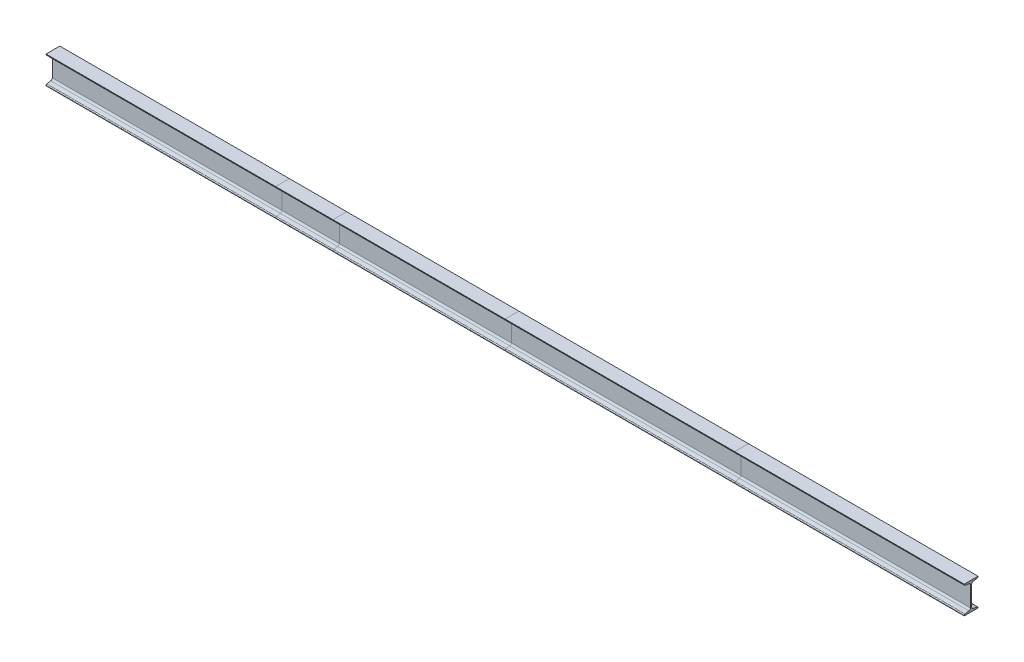
SolidWorks part; units mm, degrees
ref_plane "Front Plane" through (0, 0, 0) normal (0, 0, 1) x (1, 0, 0)
ref_plane "Top Plane" through (0, 0, 0) normal (0, 1, 0) x (1, 0, 0)
ref_plane "Right Plane" through (0, 0, 0) normal (1, 0, 0) x (0, 0, -1)
sketch "Sketch1" plane through (0, 0, 0) normal (0, 0, 1) x (1, 0, 0)
  line L0 (0, 0) -> (1000, 0)
  line L1 (1000, 0) -> (1250, 0)
  line L2 (1250, 0) -> (2000, 0)
  line L3 (2000, 0) -> (3000, 0)
  line L4 (3000, 0) -> (4000, 0)
  dimension "D1" = 1000
  dimension "D2" = 250
  dimension "D3" = 750
  dimension "D4" = 1000
  dimension "D5" = 1000
other "Sb beam 120 X 12(1)"
ref_plane "Plane1" through (0, 0, 0) normal (1, 0, 0) x (0, 0, 1)
sketch "Sketch11" plane through (0, 0, 0) normal (1, 0, 0) x (0, 0, 1)
  line L0 (-30, -60) -> (-30, -58.0801)
  line L1 (-26.6576, -54.1345) -> (-9.1847, -51.2221)
  line L2 (-2.5, -43.331) -> (-2.5, 43.331)
  line L3 (-9.1847, 51.2221) -> (-26.6576, 54.1345)
  line L4 (-30, 58.0801) -> (-30, 60)
  line L5 (-30, 60) -> (30, 60)
  line L6 (30, 60) -> (30, 58.0801)
  line L7 (26.6576, 54.1345) -> (9.1847, 51.2221)
  line L8 (2.5, 43.331) -> (2.5, -43.331)
  line L9 (9.1847, -51.2221) -> (26.6576, -54.1345)
  line L10 (30, -58.0801) -> (30, -60)
  line L11 (30, -60) -> (-30, -60)
  line L15 (-2.5, 0) -> (2.5, 0) construction
  arc A0 (-9.1847, -51.2221) -> (-2.5, -43.331) centre (-10.5, -43.331) ccw
  arc A1 (-2.5, 43.331) -> (-9.1847, 51.2221) centre (-10.5, 43.331) ccw
  arc A2 (9.1847, 51.2221) -> (2.5, 43.331) centre (10.5, 43.331) ccw
  arc A3 (2.5, -43.331) -> (9.1847, -51.2221) centre (10.5, -43.331) ccw
  arc A4 (-26.6576, 54.1345) -> (-30, 58.0801) centre (-26, 58.0801) cw
  arc A5 (26.6576, 54.1345) -> (30, 58.0801) centre (26, 58.0801) ccw
  arc A6 (-30, -58.0801) -> (-26.6576, -54.1345) centre (-26, -58.0801) cw
  arc A7 (30, -58.0801) -> (26.6576, -54.1345) centre (26, -58.0801) ccw
  point P1 (0, 60)
  point P8 (0, -60)
  point P21 (0, 0)
  point P34 (0, 0)
  dimension "RI" = 8
  dimension "D3" = 4
  dimension "BF" = 60
  dimension "D2" = 9.463
  dimension "DEPTH" = 120
  dimension "TW" = 5
  dimension "D1" = 86.662
